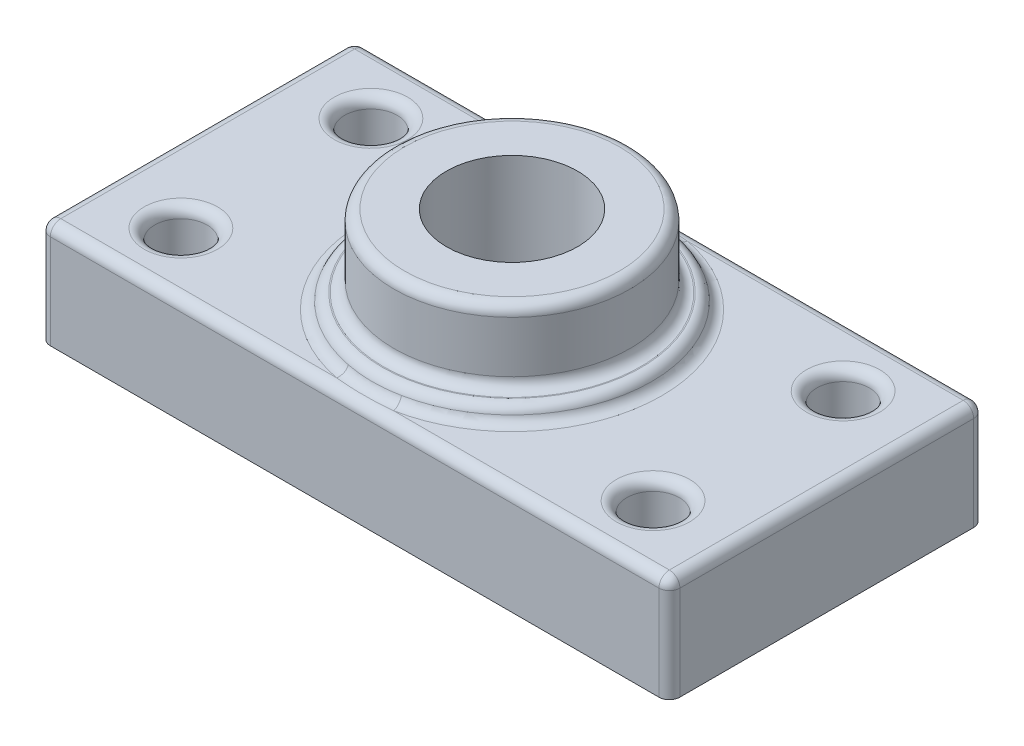
SolidWorks part; units mm, degrees
ref_plane "Front Plane" through (0, 0, 0) normal (0, 0, 1) x (1, 0, 0)
ref_plane "Top Plane" through (0, 0, 0) normal (0, 1, 0) x (1, 0, 0)
ref_plane "Right Plane" through (0, 0, 0) normal (1, 0, 0) x (0, 0, -1)
sketch "Sketch1" plane through (0, 0, 0) normal (0, 1, 0) x (1, 0, 0)
  line L0 (0, 50.212) -> (0, 0) construction
  line L1 (-76.2, 38.1) -> (76.2, 38.1)
  line L2 (-76.2, 38.1) -> (-76.2, -38.1)
  line L3 (-76.2, -38.1) -> (76.2, -38.1)
  line L4 (76.2, 38.1) -> (76.2, -38.1)
  line L5 (-76.2, 38.1) -> (76.2, -38.1) construction
  line L6 (-76.2, -38.1) -> (76.2, 38.1) construction
  line L7 (0, 0) -> (-87.9328, 0) construction
  line L8 (0, 0) -> (90.4063, 0) construction
  circle A0 centre (-57.15, 23.0035) radius 6.35
  circle A1 centre (-57.15, -23.0035) radius 6.35
  circle A2 centre (57.15, 23.0035) radius 6.35
  circle A3 centre (57.15, -23.0035) radius 6.35
  circle A4 centre (0, 0) radius 33.916
  circle A5 centre (0, 0) radius 28.575
  circle A6 centre (0, 0) radius 15.875
  point P0 (0, 0)
  dimension "D3" = 12.7
  dimension "D4" = 57.15
  dimension "D5" = 31.75
  dimension "D6" = 19.05
  dimension "D1" = 152.4
  dimension "D2" = 76.2
sketch "Sketch2" plane through (0, 0, 0) normal (0, 1, 0) x (1, 0, 0)
sketch "Sketch4" plane through (0, 0, 0) normal (0, 1, 0) x (1, 0, 0)
extrude "Boss-Extrude4" add sketch "Sketch1" along normal blind 25.4 contours L4 L1 L2 L3 A4 A3 A1 A0 A2
sketch "Sketch5" plane through (0, 0, 0) normal (0, 1, 0) x (1, 0, 0)
  circle A0 centre (0, 0) radius 33.916
  circle A1 centre (0, 0) radius 28.575
  dimension "D1" = 57.15
extrude "Boss-Extrude5" add sketch "Sketch5" along normal blind 28.956 contours A0
sketch "Sketch6" plane through (0, 0, 0) normal (0, 1, 0) x (1, 0, 0)
  circle A0 centre (0, 0) radius 28.575
  circle A1 centre (0, 0) radius 15.875
  dimension "D1" = 57.15
  dimension "D2" = 31.75
extrude "Boss-Extrude6" add sketch "Sketch6" along normal blind 46.482 contours A0
sketch "Sketch7" plane through (0, 0, 0) normal (0, 1, 0) x (1, 0, 0)
  circle A0 centre (0, 0) radius 15.875
  dimension "D1" = 31.75
extrude "Cut-Extrude2" cut sketch "Sketch7" along normal blind 51.054 and the other way blind 0.254
sketch "Sketch8" plane through (0, 0, 0) normal (0, 1, 0) x (1, 0, 0)
  line L1 (-76.2, -38.1) -> (76.2, -38.1)
  line L2 (-76.2, -38.1) -> (-76.2, 38.1)
  line L3 (-76.2, 38.1) -> (76.2, 38.1)
  line L4 (76.2, -38.1) -> (76.2, 38.1)
extrude "Boss-Extrude8" add sketch "Sketch8" along normal blind 2.54
fillet "Fillet1" radius 2.54 7 edges at (0, 46.482, 28.575) (0, 28.956, 28.575) (0, 28.956, 33.916) (76.2, 12.7, 38.1) (-76.2, 12.7, 38.1) (-76.2, 12.7, -38.1) (76.2, 12.7, -38.1)
fillet "Fillet2" radius 2.54 8 edges at (-75.4561, 25.4, -37.3561) (-76.2, 25.4, 0) (-75.4561, 25.4, 37.3561) (0, 25.4, 38.1) (75.4561, 25.4, 37.3561) (76.2, 25.4, 0) (75.4561, 25.4, -37.3561) (0, 25.4, -38.1)
fillet "Fillet3" radius 2.54 5 edges at (57.15, 25.4, -16.6535) (-57.15, 25.4, -16.6535) (-57.15, 25.4, 29.3535) (57.15, 25.4, 29.3535) (0, 25.4, 33.916)
